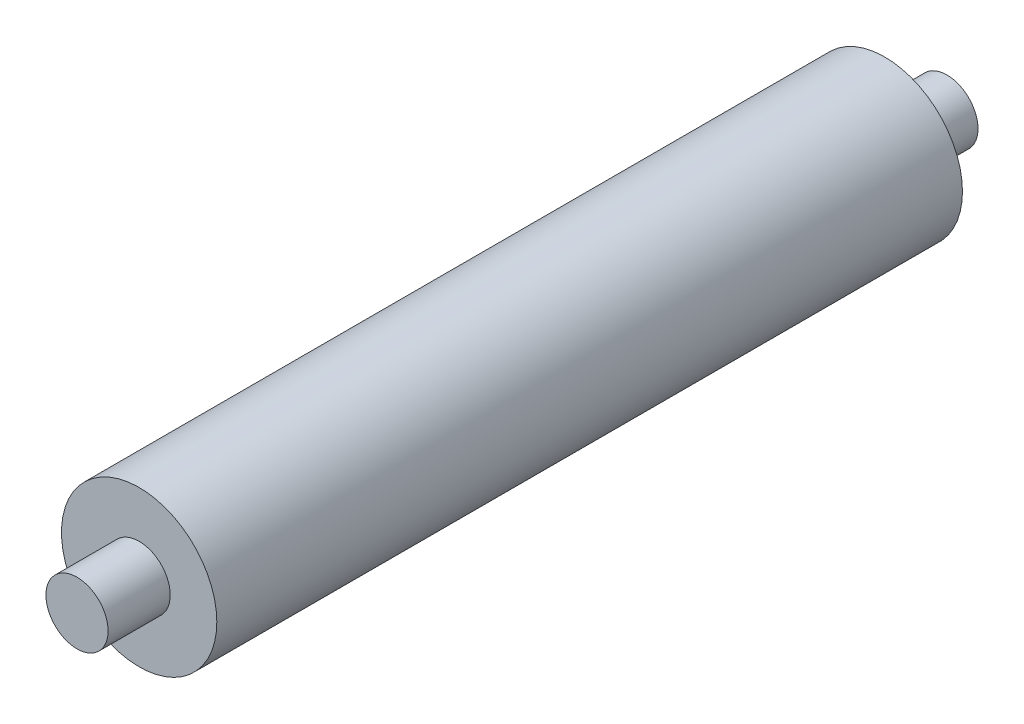
SolidWorks part; units mm, degrees
ref_plane "Front Plane" through (0, 0, 0) normal (0, 0, 1) x (1, 0, 0)
ref_plane "Top Plane" through (0, 0, 0) normal (0, 1, 0) x (1, 0, 0)
ref_plane "Right Plane" through (0, 0, 0) normal (1, 0, 0) x (0, 0, -1)
sketch "Sketch2" plane through (0, 0, 0) normal (0, 0, 1) x (1, 0, 0)
  circle A0 centre (0, 0) radius 12.5
  dimension "D1" = 25
extrude "Boss-Extrude1" add sketch "Sketch2" against normal blind 120
sketch "Sketch3" plane through (0, 0, 0) normal (0, 0, 1) x (1, 0, 0)
  circle A0 centre (0, 0) radius 5
  dimension "D1" = 10
extrude "Boss-Extrude2" add sketch "Sketch3" along normal blind 10
ref_plane "Plane1" through (0, 0, -60) normal (0, 0, 1) x (1, 0, 0)
mirror "Mirror1" about plane through (0, 0, -60) normal (0, 0, 1) of "Boss-Extrude2"
